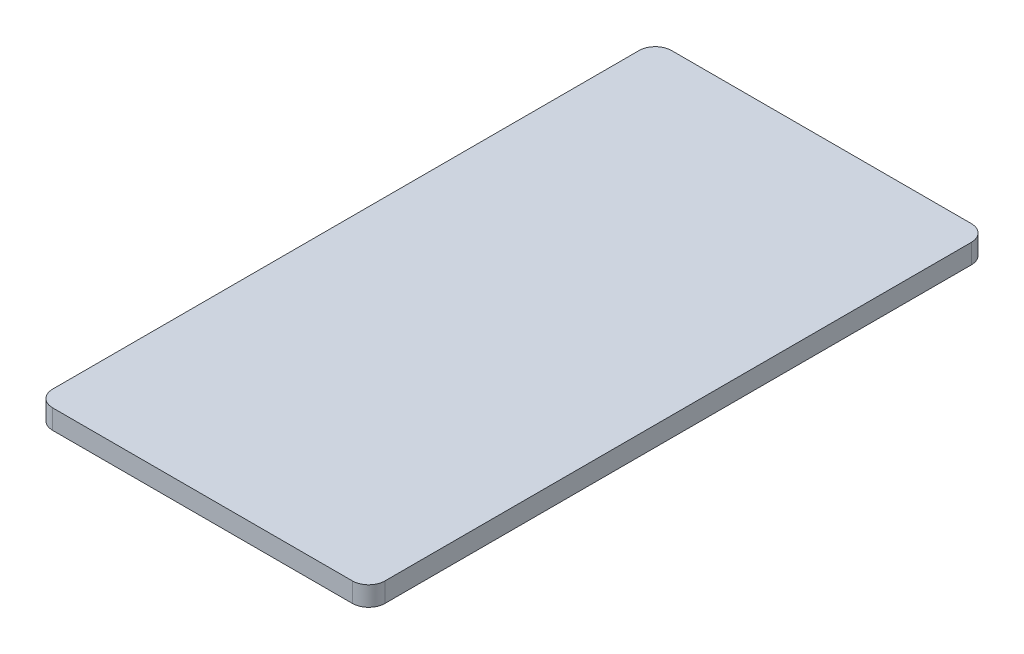
SolidWorks part; units mm, degrees
ref_plane "Front Plane" through (0, 0, 0) normal (0, 0, 1) x (1, 0, 0)
ref_plane "Top Plane" through (0, 0, 0) normal (0, 1, 0) x (1, 0, 0)
ref_plane "Right Plane" through (0, 0, 0) normal (1, 0, 0) x (0, 0, -1)
ref_plane "Plane1" through (0, 2.6, 0) normal (0, -1, 0) x (1, 0, 0)
sketch "Sketch1" plane through (0, 2.6, 0) normal (0, -1, 0) x (1, 0, 0)
  line L0 (10.4, -14) -> (10.4, 22)
  line L1 (9.4, 23) -> (-9, 23)
  line L2 (-10, 22) -> (-10, -14)
  line L3 (-9, -15) -> (9.4, -15)
  arc A0 (9.4, -15) -> (10.4, -14) centre (9.4, -14) ccw
  arc A1 (10.4, 22) -> (9.4, 23) centre (9.4, 22) ccw
  arc A2 (-9, 23) -> (-10, 22) centre (-9, 22) ccw
  arc A3 (-10, -14) -> (-9, -15) centre (-9, -14) ccw
extrude "Boss-Extrude1" add sketch "Sketch1" against normal blind 1.2
